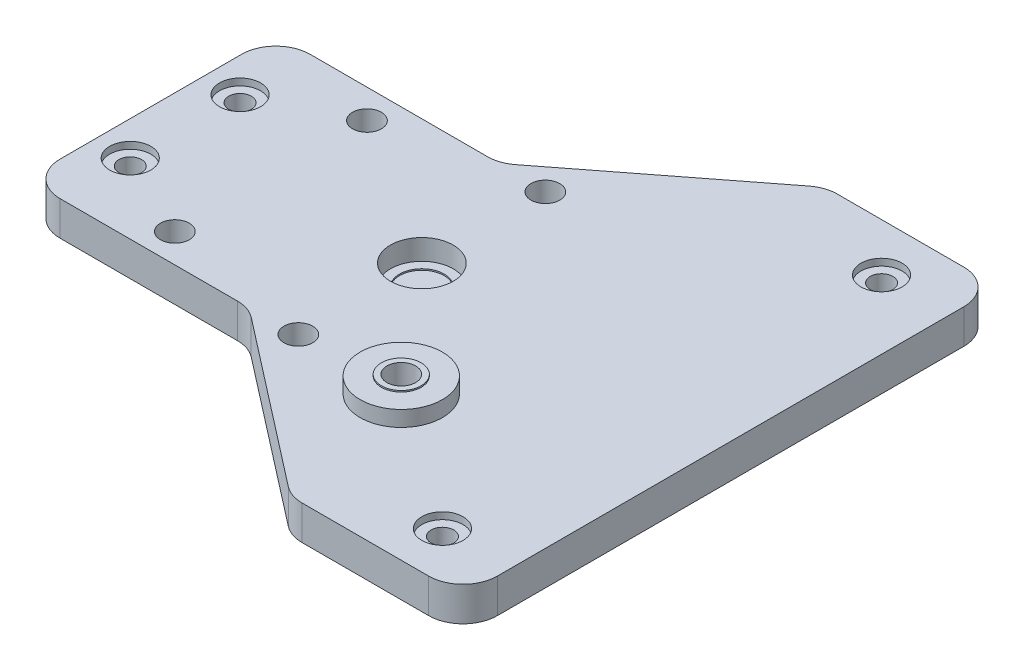
SolidWorks part; units mm, degrees
ref_plane "Front Plane" through (0, 0, 0) normal (0, 0, 1) x (1, 0, 0)
ref_plane "Top Plane" through (0, 0, 0) normal (0, 1, 0) x (1, 0, 0)
ref_plane "Right Plane" through (0, 0, 0) normal (1, 0, 0) x (0, 0, -1)
sketch "Sketch1" plane through (0, 0, 0) normal (0, 1, 0) x (1, 0, 0)
  line L0 (-22, 14) -> (-22, -14) construction
  line L1 (0, -18) -> (0, 18) construction
  line L3 (45, 30) -> (-70, 30)
  line L4 (45, 30) -> (45, -30)
  line L5 (45, -30) -> (-70, -30)
  line L6 (-70, 30) -> (-70, -30)
  circle A0 centre (-22, 14) radius 2.1
  circle A1 centre (0, 18) radius 2.1
  circle A2 centre (0, -18) radius 2.1
  circle A3 centre (-22, -14) radius 2.1
  circle A4 centre (15, -18) radius 2.1
  point P11 (-22, 0)
  point P19 (45, 0)
  dimension "D1" = 4.2
  dimension "D2" = 22
  dimension "D3" = 28
  dimension "D4" = 36
  dimension "D5" = 15
  dimension "D6" = 60
  dimension "D7" = 45
  dimension "D8" = 115
extrude "Boss-Extrude1" add sketch "Sketch1" along normal blind 5
sketch "Sketch2" plane through (0, 5, 0) normal (0, 1, 0) x (1, 0, 0)
  circle A0 centre (0, 0) radius 4.575
  dimension "D1" = 9.15
extrude "Cut-Extrude1" cut sketch "Sketch2" against normal blind 3
sketch "Sketch3" plane through (0, 2, 0) normal (0, 1, 0) x (1, 0, 0)
  circle A0 centre (0, 0) radius 3.25
  dimension "D1" = 6.5
extrude "Cut-Extrude2" cut sketch "Sketch3" against normal blind 0.2
sketch "Sketch4" plane through (0, 5, 0) normal (0, 1, 0) x (1, 0, 0)
  line L2 (-22, 18.2216) -> (-8.2975, 18.2216) construction
  line L3 (-22, -18.2216) -> (-8.2975, -18.2216) construction
  line L7 (-28.4216, 7.4) -> (-28.4216, 11.8) construction
  line L8 (-28.4216, -7.4) -> (-28.4216, 7.4) construction
  line L9 (-28.4216, -11.8) -> (-28.4216, -7.4) construction
  line L15 (-14.3288, 12.5) -> (19.3012, 38.5804) construction
  line L16 (-45, 12.5) -> (-14.3288, 12.5) construction
  line L17 (-45, -12.5) -> (-45, 12.5) construction
  line L18 (-14.3288, -12.5) -> (-45, -12.5) construction
  line L19 (19.3012, -38.5804) -> (-14.3288, -12.5) construction
  line L20 (-34.5, 8) -> (-34.5, -8) construction
  arc A2 (-22, 18.2216) -> (-28.4216, 11.8) centre (-22, 11.8) ccw construction
  arc A3 (-28.4216, -11.8) -> (-22, -18.2216) centre (-22, -11.8) ccw construction
  arc A6 (-8.2975, 18.2216) -> (-3.0173, 20.626) centre (-8.2975, 25.2216) ccw construction
  arc A7 (-3.0173, -20.626) -> (-8.2975, -18.2216) centre (-8.2975, -25.2216) ccw construction
  circle A8 centre (-34.5, 8) radius 3 construction
  circle A9 centre (-34.5, -8) radius 3 construction
  circle A10 centre (-34.5, -8) radius 1.65
  circle A11 centre (-34.5, 8) radius 1.65
  point P26 (-34.5, 0)
  dimension "D1" = 6
  dimension "D2" = 3.3
  dimension "D3" = 16
  dimension "D4" = 34.5
extrude "Cut-Extrude3" cut sketch "Sketch4" against normal through all
sketch "Sketch6" plane through (0, 5, 0) normal (0, 1, 0) x (1, 0, 0)
  line L0 (-22, 18.2216) -> (-34.5, 18.2216)
  line L1 (-39.5, 13.2216) -> (-39.5, -13.2216)
  line L2 (-34.5, -18.2216) -> (-22, -18.2216)
  line L4 (-70, -30) -> (45, -30) construction
  line L5 (-22, -30) -> (-70, -30)
  line L6 (-70, -30) -> (-70, 30)
  line L7 (-70, 30) -> (-70, -30) construction
  line L8 (45, 30) -> (-70, 30) construction
  line L9 (-70, 30) -> (-22, 30)
  line L11 (-34.5, 8) -> (-34.5, -8) construction
  line L12 (-22, -18.2216) -> (-8.2975, -18.2216) construction
  line L13 (-22, 18.2216) -> (-8.2975, 18.2216) construction
  line L14 (-22, 18.2216) -> (-8.2975, 18.2216)
  line L15 (-22, -18.2216) -> (-8.2975, -18.2216)
  line L22 (19.3012, 38.5804) -> (-22, 30)
  line L23 (19.3012, -38.5804) -> (-22, -30)
  line L25 (-8.2975, 18.2216) -> (-6.951, 18.2216)
  line L26 (-14.3288, 12.5) -> (19.3012, 38.5804) construction
  line L27 (-6.951, 18.2216) -> (19.3012, 38.5804)
  line L28 (-8.2975, -18.2216) -> (-6.951, -18.2216)
  line L29 (-6.951, -18.2216) -> (19.3012, -38.5804)
  line L30 (19.3012, -38.5804) -> (-14.3288, -12.5) construction
  arc A0 (-34.5, 18.2216) -> (-39.5, 13.2216) centre (-34.5, 13.2216) ccw
  arc A1 (-39.5, -13.2216) -> (-34.5, -18.2216) centre (-34.5, -13.2216) ccw
  dimension "D2" = 5
  dimension "D1" = 5
extrude "Cut-Extrude4" cut sketch "Sketch6" against normal through all
sketch "Sketch7" plane through (0, 5, 0) normal (0, 1, 0) x (1, 0, 0)
  line L0 (19.8422, 39) -> (8.2369, 30)
  line L1 (8.2369, 30) -> (45, 30)
  line L2 (45, 30) -> (45, 39)
  line L3 (45, -30) -> (8.2369, -30)
  line L4 (8.2369, -30) -> (19.8422, -39)
  line L5 (19.8422, -39) -> (45, -39)
  line L6 (45, -39) -> (45, -30)
  line L7 (45, 39) -> (19.8422, 39)
  line L10 (-14.3288, 12.5) -> (19.3012, 38.5804) construction
  line L11 (45, 30) -> (8.2369, 30) construction
  line L12 (19.3012, -38.5804) -> (-14.3288, -12.5) construction
  line L13 (8.2369, -30) -> (45, -30) construction
  dimension "D1" = 78
extrude "Boss-Extrude2" add sketch "Sketch7" against normal up to surface (5 mm away) up to face at (-5.7499, 0, 0)
sketch "Sketch8" plane through (0, 5, 0) normal (0, 1, 0) x (1, 0, 0)
  line L0 (35, 32) -> (35, -32) construction
  circle A0 centre (35, 32) radius 1.65
  circle A1 centre (35, -32) radius 1.65
  circle A2 centre (35, 32) radius 3 construction
  circle A3 centre (35, -32) radius 3 construction
  point P6 (35, 0)
  dimension "D1" = 6
  dimension "D2" = 3.3
  dimension "D3" = 35
  dimension "D4" = 64
extrude "Cut-Extrude5" cut sketch "Sketch8" against normal through all
fillet "Fillet1" radius 5 6 edges at (45, 2.5, 39) (19.8422, 2.5, 39) (19.8422, 2.5, -39) (45, 2.5, -39) (-6.951, 2.5, 18.2216) (-6.951, 2.5, -18.2216)
sketch "Sketch9" plane through (0, 5, 0) normal (0, 1, 0) x (1, 0, 0)
  circle A0 centre (15, -18) radius 6
  circle A1 centre (15, -18) radius 2.1 construction
  circle A2 centre (15, -18) radius 2.1
  dimension "D1" = 12
extrude "Boss-Extrude3" add sketch "Sketch9" along normal blind 2.275
sketch "Sketch10" plane through (0, 7.275, 0) normal (0, 1, 0) x (1, 0, 0)
  circle A0 centre (15, -18) radius 2.9
  circle A1 centre (15, -18) radius 2.1 construction
  circle A2 centre (15, -18) radius 2.1
  dimension "D1" = 0.8
extrude "Boss-Extrude4" add sketch "Sketch10" along normal blind 0.2
sketch "Sketch11" plane through (0, 5, 0) normal (0, 1, 0) x (1, 0, 0)
  circle A0 centre (-34.5, 8) radius 3
  circle A1 centre (-34.5, -8) radius 3
  circle A2 centre (35, -32) radius 3
  circle A3 centre (35, 32) radius 3
  dimension "D1" = 6
extrude "Cut-Extrude6" cut sketch "Sketch11" against normal blind 1
